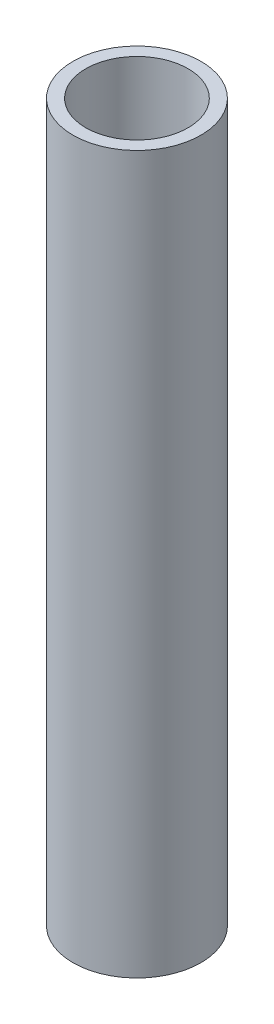
SolidWorks part; units mm, degrees
ref_plane "Alzado" through (0, 0, 0) normal (0, 0, 1) x (1, 0, 0)
ref_plane "Planta" through (0, 0, 0) normal (0, 1, 0) x (1, 0, 0)
ref_plane "Vista lateral" through (0, 0, 0) normal (1, 0, 0) x (0, 0, -1)
sketch "Croquis1" plane through (0, 0, 0) normal (0, 1, 0) x (1, 0, 0)
  circle A0 centre (0, 0) radius 12.5
  circle A1 centre (0, 0) radius 10
  dimension "D1" = 25
  dimension "D2" = 20
extrude "Saliente-Extruir1" add sketch "Croquis1" along normal mid plane 140
